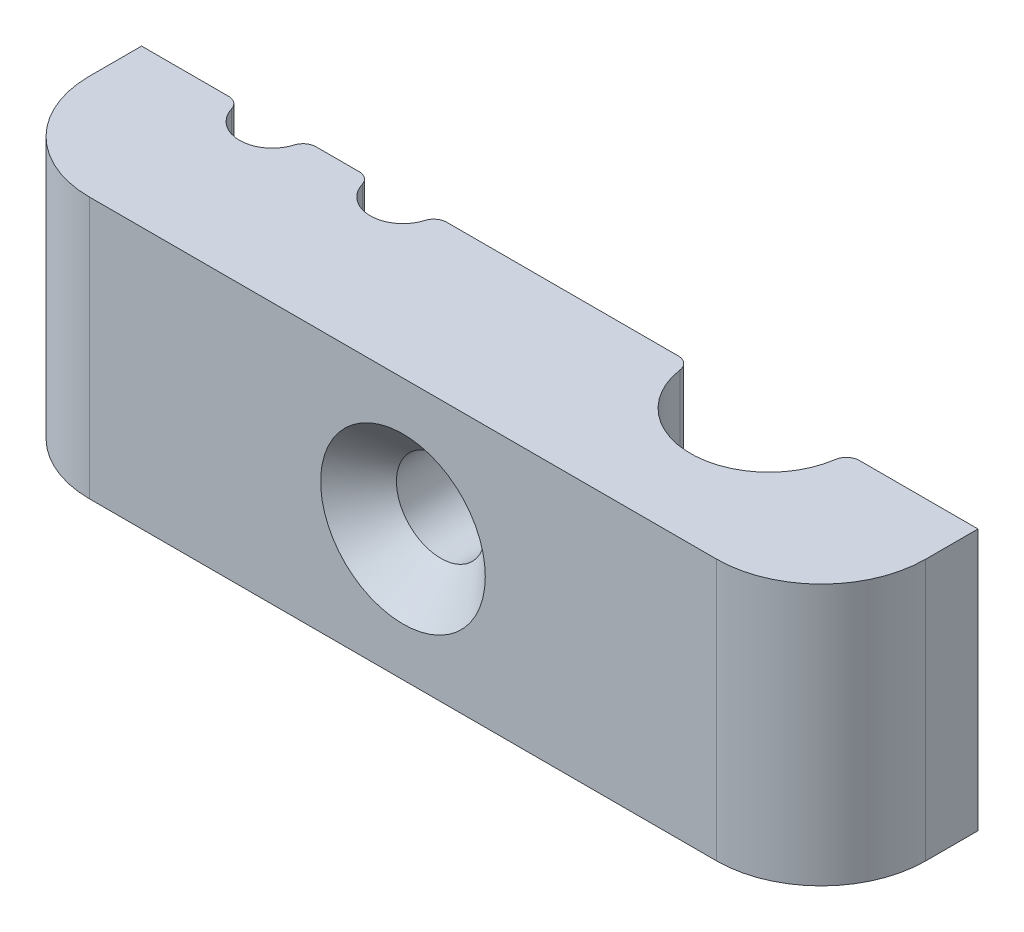
SolidWorks part; units mm, degrees
ref_plane "Front Plane" through (0, 0, 0) normal (0, 0, 1) x (1, 0, 0)
ref_plane "Top Plane" through (0, 0, 0) normal (0, 1, 0) x (1, 0, 0)
ref_plane "Right Plane" through (0, 0, 0) normal (1, 0, 0) x (0, 0, -1)
sketch "Sketch1" plane through (0, 0, 0) normal (0, 0, 1) x (1, 0, 0)
  line L1 (-16, -5) -> (16, -5)
  line L2 (-16, -5) -> (-16, 5)
  line L3 (-16, 5) -> (16, 5)
  line L4 (16, -5) -> (16, 5)
  line L5 (-16, -5) -> (16, 5) construction
  line L6 (-16, 5) -> (16, -5) construction
  point P0 (0, 0)
  dimension "D1" = 32
  dimension "D2" = 10
extrude "Boss-Extrude1" add sketch "Sketch1" along normal blind 6
fillet "Fillet1" radius 4 2 edges at (16, 0, 6) (-16, 0, 6)
sketch "Sketch2" plane through (0, 0, 0) normal (0, 1, 0) x (1, 0, 0)
  line L0 (0, -6) -> (0, 0)
  line L1 (0, 0) -> (1.7, 0)
  line L2 (1.7, 0) -> (1.7, -4.55)
  line L3 (1.7, -4.55) -> (3.15, -6)
  line L4 (3.15, -6) -> (0, -6)
  line L5 (-1.7, -4.55) -> (-3.15, -6) construction
  line L6 (0, -12.35) -> (0, 101.95) construction
  line L7 (-12, -6) -> (12, -6) construction
  line L8 (16, -2) -> (16, 0) construction
  dimension "D1" = 3.4
  dimension "D2" = 6
  dimension "D3" = 6.3
  dimension "D4" = 90
  dimension "D5" = 16
revolve "Cut-Revolve1" cut sketch "Sketch2" angle 360 about L6
sketch "Sketch3" plane through (0, 0, 0) normal (0, 1, 0) x (1, 0, 0)
  line L0 (-16, 0) -> (16, 0) construction
  line L1 (-16, -2) -> (-16, 0) construction
  circle A0 centre (-11, 0) radius 1.25
  circle A1 centre (-6, 0) radius 1.25
  circle A2 centre (8, 0) radius 3
  dimension "D1" = 2.5
  dimension "D4" = 6
  dimension "D2" = 5
  dimension "D3" = 5
  dimension "D5" = 14
extrude "Cut-Extrude1" cut sketch "Sketch3" against normal through all both and the other way through all
fillet "Fillet2" radius 0.5 6 edges at (5, 0, 0) (11, 0, 0) (-7.25, 0, 0) (-4.75, 0, 0) (-12.25, 0, 0) (-9.75, 0, 0)
